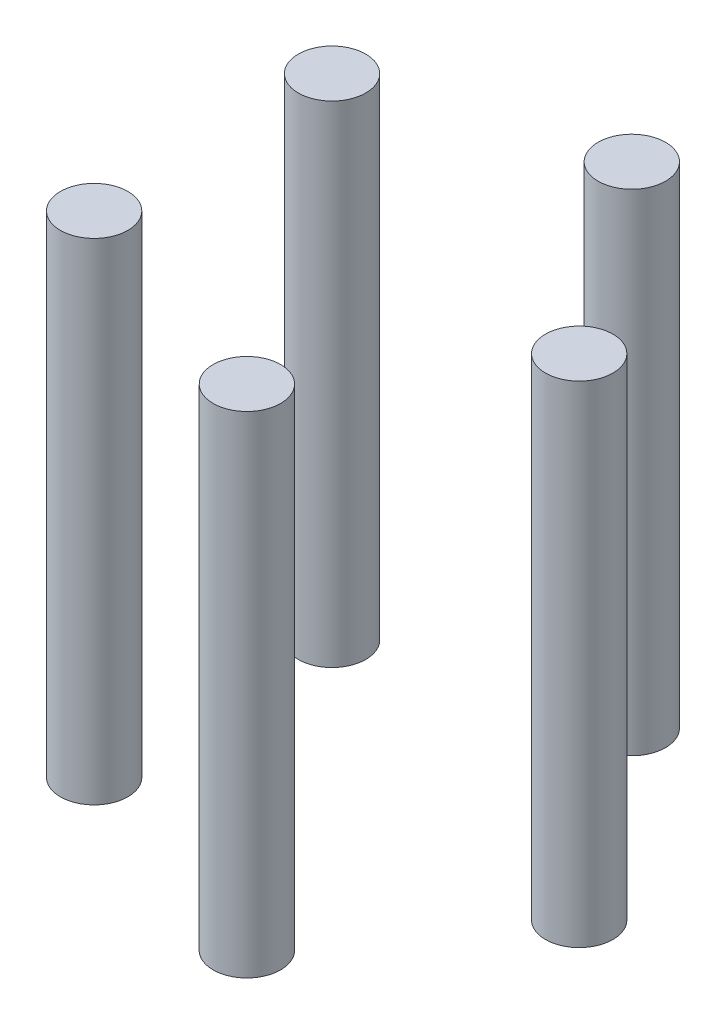
SolidWorks part; units mm, degrees
ref_plane "Front Plane" through (0, 0, 0) normal (0, 0, 1) x (1, 0, 0)
ref_plane "Top Plane" through (0, 0, 0) normal (0, 1, 0) x (1, 0, 0)
ref_plane "Right Plane" through (0, 0, 0) normal (1, 0, 0) x (0, 0, -1)
sketch "Sketch1" plane through (0, 0, 0) normal (0, 1, 0) x (1, 0, 0)
  circle A1 centre (33, 0) radius 5.5
  circle A2 centre (10.1976, -31.3849) radius 5.5
  circle A3 centre (-26.6976, -19.3969) radius 5.5
  circle A4 centre (-26.6976, 19.3969) radius 5.5
  circle A5 centre (10.1976, 31.3849) radius 5.5
  circle A21 centre (0, 0) radius 33
  point P45 (0, 0)
  dimension "D1" = 5
extrude "Boss-Extrude1" add sketch "Sketch1" along normal blind 80 contours A3 A21 | A21 A3 | A21 A4 | A4 A21 | A21 A5 | A5 A21 | A21 A1 | A1 A21 | A2 A21 | A21 A2
